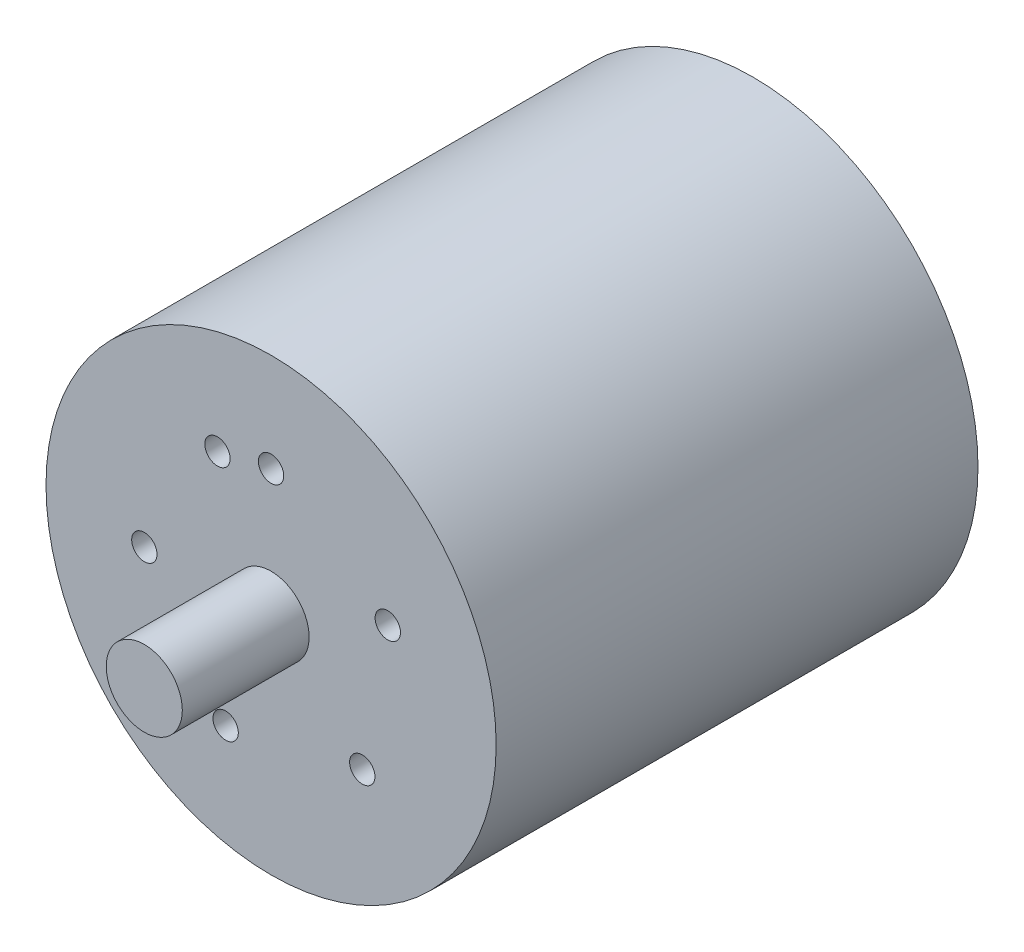
SolidWorks part; units mm, degrees
ref_plane "Front Plane" through (0, 0, 0) normal (0, 0, 1) x (1, 0, 0)
ref_plane "Top Plane" through (0, 0, 0) normal (0, 1, 0) x (1, 0, 0)
ref_plane "Right Plane" through (0, 0, 0) normal (1, 0, 0) x (0, 0, -1)
sketch "Sketch1" plane through (0, 0, 0) normal (0, 0, 1) x (1, 0, 0)
  circle A0 centre (0, 0) radius 17.75
  dimension "D1" = 35.5
extrude "Boss-Extrude1" add sketch "Sketch1" along normal mid plane 38
sketch "Sketch2" plane through (0, 0, 19) normal (0, 0, 1) x (1, 0, 0)
  circle A0 centre (0, 0) radius 3
  dimension "D1" = 6
extrude "Boss-Extrude2" add sketch "Sketch2" along normal blind 10
sketch "Sketch3" plane through (0, 0, 19) normal (0, 0, 1) x (1, 0, 0)
  circle A0 centre (0, 10) radius 1
  dimension "D1" = 2
  dimension "D2" = 10
extrude "Cut-Extrude1" cut sketch "Sketch3" against normal blind 2
pattern_circular "CirPattern1" count 6 every 67 about axis through (0, 0, 0) along (0, 0, 1) of "Cut-Extrude1"
